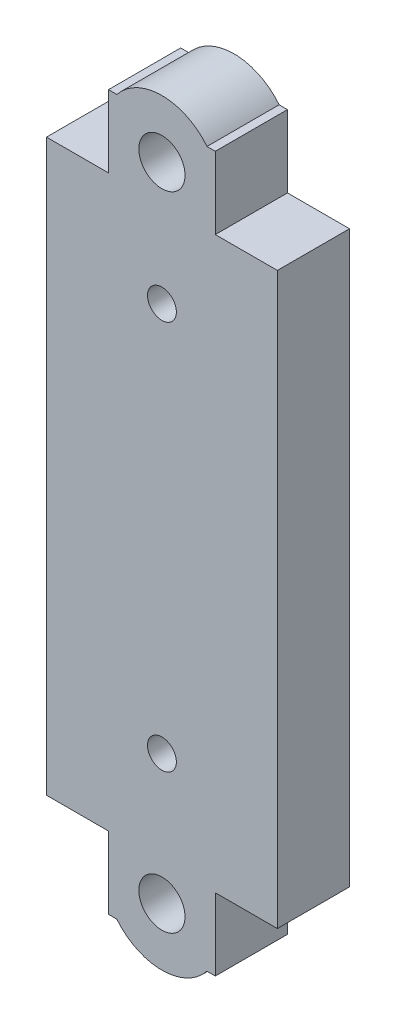
SolidWorks part; units mm, degrees
ref_plane "Plan de face" through (0, 0, 0) normal (0, 0, 1) x (1, 0, 0)
ref_plane "Plan de dessus" through (0, 0, 0) normal (0, 1, 0) x (1, 0, 0)
ref_plane "Plan de droite" through (0, 0, 0) normal (1, 0, 0) x (0, 0, -1)
sketch "Esquisse1" plane through (0, 0, 0) normal (0, 0, 1) x (1, 0, 0)
  line L0 (-14.988, -32.8409) -> (-14.988, -37.8409)
  line L1 (-17.988, 14.6591) -> (4.012, 14.6591)
  line L3 (-17.988, -40.8409) -> (4.012, -40.8409)
  line L4 (4.012, 14.6591) -> (4.012, -40.8409)
  line L5 (-3.988, 11.6591) -> (1.012, 11.6591)
  line L6 (-3.988, 11.6591) -> (-3.988, 6.6591)
  line L7 (-3.988, 6.6591) -> (1.012, 6.6591)
  line L8 (1.012, 11.6591) -> (1.012, 6.6591)
  line L9 (-3.988, -32.8409) -> (1.012, -32.8409)
  line L10 (-3.988, -32.8409) -> (-3.988, -37.8409)
  line L11 (-3.988, -37.8409) -> (1.012, -37.8409)
  line L12 (1.012, -32.8409) -> (1.012, -37.8409)
  line L13 (-9.988, -37.8409) -> (-14.988, -37.8409)
  line L14 (-9.988, -32.8409) -> (-9.988, -37.8409)
  line L15 (-9.988, -32.8409) -> (-14.988, -32.8409)
  line L16 (-14.988, 11.6591) -> (-14.988, 6.6591)
  line L17 (-9.988, 6.6591) -> (-14.988, 6.6591)
  line L18 (-9.988, 11.6591) -> (-9.988, 6.6591)
  line L19 (-9.988, 11.6591) -> (-14.988, 11.6591)
  line L20 (-17.988, 14.6591) -> (-17.988, -40.8409)
  circle A2 centre (-6.988, 0.6591) radius 1
  circle A3 centre (-6.988, -26.3409) radius 1
  point P12 (-1.488, -37.8409)
  dimension "D11" = 27
  dimension "D14" = 2
  dimension "D13" = 2
  dimension "D1" = 5
  dimension "D2" = 5
  dimension "D3" = 5
  dimension "D4" = 5
  dimension "D5" = 3
  dimension "D6" = 3
  dimension "D8" = 3
  dimension "D10" = 39.5
extrude "Boss.-Extru.1" add sketch "Esquisse1" along normal blind 5
sketch "Sketch1" plane through (0, 0, 5) normal (0, 0, 1) x (1, 0, 0)
  line L0 (-17.988, -40.8409) -> (4.012, -40.8409) construction
  line L1 (-9.988, -37.8409) -> (-9.988, -32.8409) construction
  line L7 (-3.988, 11.6591) -> (-3.988, 6.6591) construction
  line L21 (1.012, -37.8409) -> (-14.988, -37.8409)
  line L22 (1.012, -37.8409) -> (1.012, 11.6591)
  line L23 (1.012, 11.6591) -> (-14.988, 11.6591)
  line L24 (-14.988, -37.8409) -> (-14.988, 11.6591)
  line L25 (4.012, -40.8409) -> (-17.988, -40.8409)
  line L26 (4.012, -40.8409) -> (4.012, 14.6591)
  line L27 (4.012, 14.6591) -> (-17.988, 14.6591)
  line L28 (-17.988, -40.8409) -> (-17.988, 14.6591)
extrude "Cut-Extrude1" cut sketch "Sketch1" against normal blind 10
sketch "Sketch2" plane through (0, 0, 5) normal (0, 0, 1) x (1, 0, 0)
  line L0 (-9.988, -32.8409) -> (-14.988, -32.8409) construction
  line L1 (-2.988, -37.8409) -> (-3.988, -37.8409)
  line L2 (-2.988, -37.8409) -> (-2.988, -32.8409)
  line L3 (-2.988, -32.8409) -> (-3.988, -32.8409)
  line L4 (-3.988, -37.8409) -> (-3.988, -32.8409)
  line L5 (-9.988, -37.8409) -> (-10.988, -37.8409)
  line L6 (-9.988, -37.8409) -> (-9.988, -32.8409)
  line L7 (-9.988, -32.8409) -> (-10.988, -32.8409)
  line L8 (-10.988, -37.8409) -> (-10.988, -32.8409)
  line L9 (-10.988, -32.8409) -> (-10.988, -37.8409) construction
  line L11 (-3.988, 6.6591) -> (-2.988, 6.6591)
  line L12 (-3.988, 6.6591) -> (-3.988, 11.6591)
  line L13 (-3.988, 11.6591) -> (-2.988, 11.6591)
  line L14 (-2.988, 6.6591) -> (-2.988, 11.6591)
  line L15 (-9.988, 6.6591) -> (-10.988, 6.6591)
  line L16 (-9.988, 6.6591) -> (-9.988, 11.6591)
  line L17 (-9.988, 11.6591) -> (-10.988, 11.6591)
  line L18 (-10.988, 6.6591) -> (-10.988, 11.6591)
extrude "Boss-Extrude1" add sketch "Sketch2" against normal up to vertex (5 mm away)
sketch "Sketch3" plane through (0, 0, 5) normal (0, 0, 1) x (1, 0, 0)
  line L0 (-10.988, -37.8409) -> (-2.988, -37.8409) construction
  line L1 (-2.988, -37.8409) -> (-2.988, -32.8409) construction
  line L2 (-2.988, 6.6591) -> (-2.988, 11.6591) construction
  circle A0 centre (-6.988, -35.3409) radius 1.6
  circle A1 centre (-6.988, 9.1591) radius 1.6
  point P7 (-6.988, -37.8409)
  point P10 (-2.988, -35.3409)
  point P14 (-2.988, 9.1591)
  dimension "D1" = 3.2
  dimension "D2" = 3.2
extrude "Cut-Extrude2" cut sketch "Sketch3" against normal blind 10
sketch "Sketch4" plane through (0, 0, 5) normal (0, 0, 1) x (1, 0, 0)
  circle A0 centre (-6.988, -35.3409) radius 1.6
  circle A1 centre (-6.988, -35.3409) radius 4
  circle A2 centre (-6.988, 9.1591) radius 1.6
  circle A3 centre (-6.988, 9.1591) radius 4
extrude "Boss-Extrude2" add sketch "Sketch4" against normal up to vertex (5 mm away)
sketch "Sketch5" plane through (0, 0, 5) normal (0, 0, 1) x (1, 0, 0)
  line L0 (-2.988, 11.6591) -> (-3.8655, 11.6591) construction
  line L1 (-2.988, -37.8409) -> (-3.288, -37.8409)
  line L2 (-2.988, -37.8409) -> (-2.988, -32.8409)
  line L3 (-2.988, -32.8409) -> (-3.288, -32.8409)
  line L4 (-3.288, -37.8409) -> (-3.288, -32.8409)
  line L5 (-10.988, -37.8409) -> (-10.688, -37.8409)
  line L6 (-10.988, -37.8409) -> (-10.988, -32.8409)
  line L7 (-10.988, -32.8409) -> (-10.688, -32.8409)
  line L8 (-10.688, -37.8409) -> (-10.688, -32.8409)
  line L9 (-2.988, 6.6591) -> (-3.288, 6.6591)
  line L10 (-2.988, 6.6591) -> (-2.988, 11.6591)
  line L11 (-2.988, 11.6591) -> (-3.288, 11.6591)
  line L12 (-3.288, 6.6591) -> (-3.288, 11.6591)
  line L13 (1.012, -32.8409) -> (-2.988, -32.8409) construction
  line L14 (-10.988, 11.6591) -> (-10.688, 11.6591)
  line L15 (-10.988, 11.6591) -> (-10.988, 6.6591)
  line L16 (-10.988, 6.6591) -> (-10.688, 6.6591)
  line L17 (-10.688, 11.6591) -> (-10.688, 6.6591)
extrude "Cut-Extrude3" cut sketch "Sketch5" against normal blind 10
move or copy body "Body-Move/Copy1" [suppressed] bodies to move or copy 101
